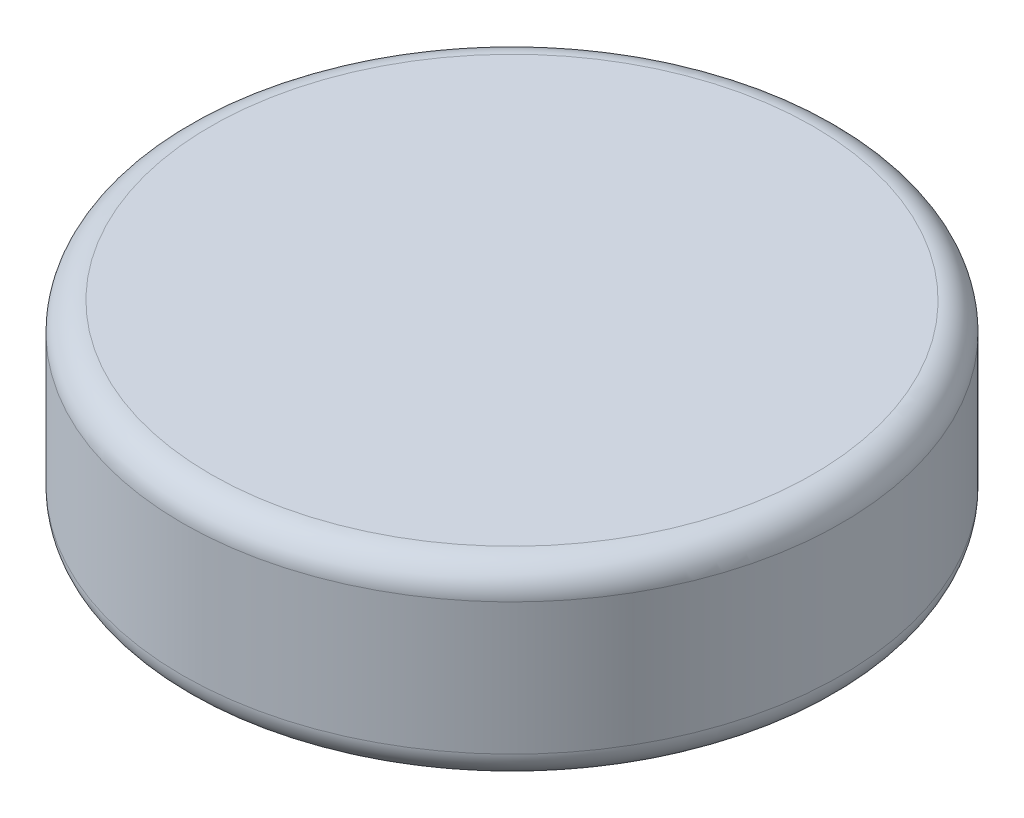
SolidWorks part; units mm, degrees
material "Plain Carbon Steel"
ref_plane "Front Plane" through (0, 0, 0) normal (0, 0, 1) x (1, 0, 0)
ref_plane "Top Plane" through (0, 0, 0) normal (0, 1, 0) x (1, 0, 0)
ref_plane "Right Plane" through (0, 0, 0) normal (1, 0, 0) x (0, 0, -1)
sketch "Sketch1" plane through (0, 0, 0) normal (0, 1, 0) x (1, 0, 0)
  circle A0 centre (0, 0) radius 3.5
  dimension "D1" = 7
extrude "Boss-Extrude1" add sketch "Sketch1" along normal blind 2
fillet "Fillet1" radius 0.3 2 edges at (0, 0, 3.5) (0, 2, 3.5)
